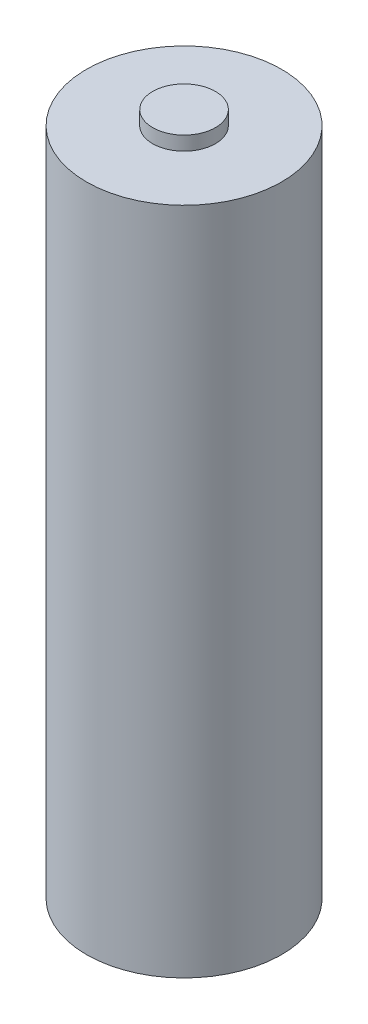
SolidWorks part; units mm, degrees
material "Custom Aluminium"
ref_plane "Front Plane" through (0, 0, 0) normal (0, 0, 1) x (1, 0, 0)
ref_plane "Top Plane" through (0, 0, 0) normal (0, 1, 0) x (1, 0, 0)
ref_plane "Right Plane" through (0, 0, 0) normal (1, 0, 0) x (0, 0, -1)
sketch "Sketch1" plane through (0, 0, 0) normal (0, 1, 0) x (1, 0, 0)
  circle A0 centre (0, 0) radius 7
  dimension "D1" = 14
extrude "Boss-Extrude1" add sketch "Sketch1" along normal blind 48
sketch "Sketch2" plane through (0, 48, 0) normal (0, 1, 0) x (1, 0, 0)
  circle A0 centre (0, 0) radius 2.25
  dimension "D1" = 4.5
extrude "Boss-Extrude2" add sketch "Sketch2" along normal blind 1
sketch "Sketch3" plane through (0, 0, 0) normal (0, 1, 0) x (1, 0, 0)
  circle A0 centre (0, 0) radius 4.5
  dimension "D1" = 9
extrude "Boss-Extrude3" add sketch "Sketch3" against normal blind 0.5
sketch "Sketch4" plane through (0, 0, 0) normal (0, 1, 0) x (1, 0, 0)
  circle A0 centre (0, 0) radius 3
  circle A1 centre (0, 0) radius 2.5
  dimension "D1" = 6
  dimension "D2" = 5
extrude "Cut-Extrude1" cut sketch "Sketch4" against normal through all
